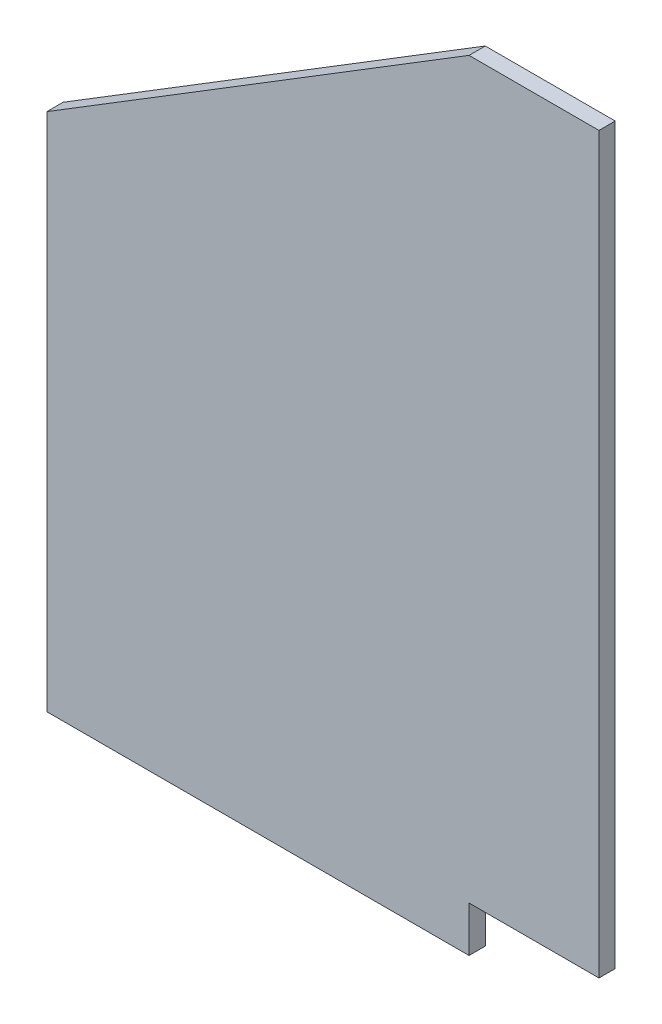
SolidWorks part; units mm, degrees
material "A-Glass Fiber"
ref_plane "Front Plane" through (0, 0, 0) normal (0, 0, 1) x (1, 0, 0)
ref_plane "Top Plane" through (0, 0, 0) normal (0, 1, 0) x (1, 0, 0)
ref_plane "Right Plane" through (0, 0, 0) normal (1, 0, 0) x (0, 0, -1)
sketch "Sketch1" plane through (0, 0, 0) normal (0, 0, 1) x (1, 0, 0)
  line L0 (0, 0) -> (0, 143.51)
  line L1 (0, 143.51) -> (-25.4, 143.51)
  line L3 (-107.95, -8.89) -> (-25.4, -8.89)
  line L4 (-25.4, -8.89) -> (-25.4, 0)
  line L5 (-25.4, 0) -> (0, 0)
  line L6 (-107.95, -8.89) -> (-107.95, 92.71)
  line L7 (-107.95, 92.71) -> (-25.4, 143.51)
  dimension "D2" = 82.55
  dimension "D3" = 25.4
  dimension "D5" = 25.4
  dimension "D6" = 101.6
  dimension "D4" = 152.4
  dimension "D1" = 8.89
extrude "Boss-Extrude1" add sketch "Sketch1" along normal blind 3.175
equation "\"Tab Height\"= 1.00"
equation "\"Trailing Edge\"= 3.25"
equation "\"Tip Chord\"= 4"
equation "\"Root Chord\"= 6"
equation "\"Insert Height\"= 0.35"
equation "\"D1@Sketch1\"=\"Insert Height\""
equation "\"D5@Sketch1\"=\"Tab Height\""
equation "\"D3@Sketch1\"=\"Tab Height\""
equation "\"D2@Sketch1\"=\"Trailing Edge\""
equation "\"D4@Sketch1\"=\"Root Chord\""
equation "\"D6@Sketch1\"=\"Tip Chord\""
equation "\"Fin Thickness\"= 0.125"
equation "\"D1@Boss-Extrude1\"=\"Fin Thickness\""
